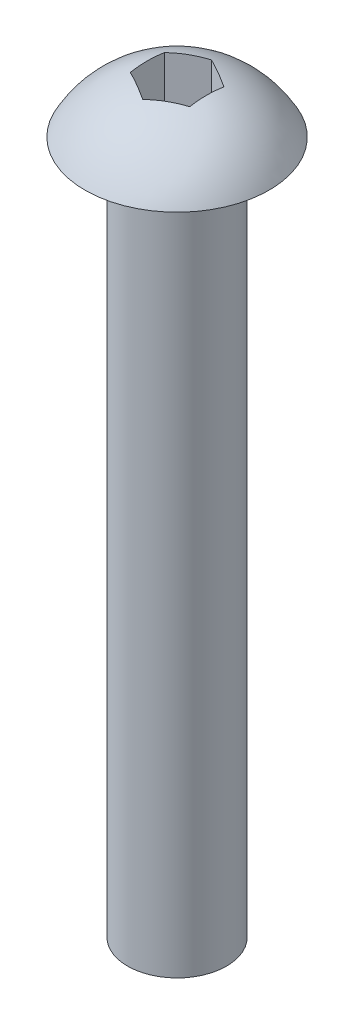
SolidWorks part; units mm, degrees
ref_plane "Front Plane" through (0, 0, 0) normal (0, 0, 1) x (1, 0, 0)
ref_plane "Top Plane" through (0, 0, 0) normal (0, 1, 0) x (1, 0, 0)
ref_plane "Right Plane" through (0, 0, 0) normal (1, 0, 0) x (0, 0, -1)
sketch "Sketch1" plane through (0, 0, 0) normal (0, 0, 1) x (1, 0, 0)
  line L0 (0, 0) -> (0, -35)
  line L1 (0, -35) -> (2.5, -35)
  line L2 (2.5, -35) -> (2.5, 0)
  line L3 (2.5, 0) -> (4.65, 0)
  line L4 (0, 0) -> (0, 2.8)
  arc A0 (0, 2.8) -> (4.65, 0) centre (0, -2.4612) cw
  dimension "D1" = 4.65
  dimension "D2" = 2.8
  dimension "D3" = 2.5
  dimension "D4" = 35
revolve "Revolve1" add sketch "Sketch1" angle 360 about L0
sketch "Sketch2" plane through (0, 0, 0) normal (0, 1, 0) x (1, 0, 0)
  line L1 (0, 1.7321) -> (-1.5, 0.866)
  line L2 (-1.5, 0.866) -> (-1.5, -0.866)
  line L3 (-1.5, -0.866) -> (0, -1.7321)
  line L4 (0, -1.7321) -> (1.5, -0.866)
  line L5 (1.5, -0.866) -> (1.5, 0.866)
  line L6 (1.5, 0.866) -> (0, 1.7321)
  circle A0 centre (0, 0) radius 1.5 construction
  dimension "D1" = 3
extrude "Cut-Extrude1" cut sketch "Sketch2" along normal blind 10
